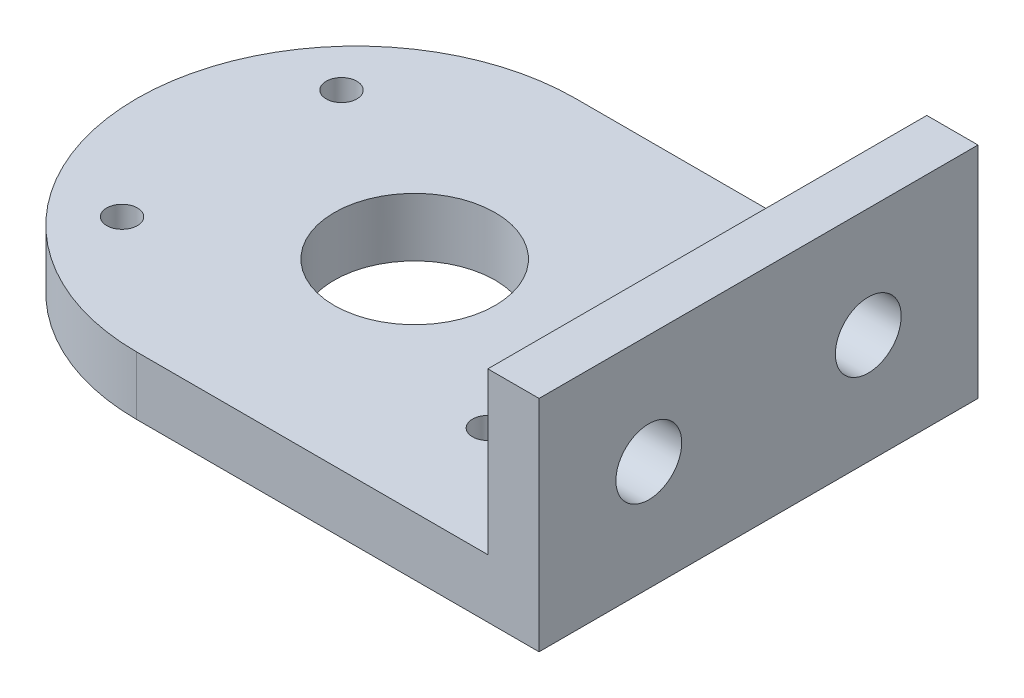
SolidWorks part; units mm, degrees
ref_plane "前视基准面" through (0, 0, 0) normal (0, 0, 1) x (1, 0, 0)
ref_plane "上视基准面" through (0, 0, 0) normal (0, 1, 0) x (1, 0, 0)
ref_plane "右视基准面" through (0, 0, 0) normal (1, 0, 0) x (0, 0, -1)
sketch "草图1" plane through (0, 0, 0) normal (0, 1, 0) x (1, 0, 0)
  line L1 (-14.75, 30) -> (40.25, 30)
  line L3 (-14.75, -30) -> (40.25, -30)
  line L4 (40.25, 30) -> (40.25, -30)
  arc A0 (-14.75, 30) -> (-14.75, -30) centre (-14.75, 0) ccw
  point P0 (0, 0)
  dimension "D4" = 55
  dimension "D1" = 60
  dimension "D2" = 40.25
  dimension "D3" = 30
extrude "凸台-拉伸1" add sketch "草图1" along normal blind 8
sketch "草图2" plane through (0, 8, 0) normal (0, 1, 0) x (1, 0, 0)
  line L0 (-14.75, -30) -> (40.25, -30) construction
  line L1 (40.25, 30) -> (33.25, 30)
  line L2 (40.25, 30) -> (40.25, -30)
  line L3 (40.25, -30) -> (33.25, -30)
  line L4 (33.25, 30) -> (33.25, -30)
  dimension "D1" = 7
extrude "凸台-拉伸2" add sketch "草图2" along normal blind 22
sketch "草图3" plane through (40.25, 0, 0) normal (1, 0, 0) x (0, 0, -1)
  line L0 (-15, 15) -> (15, 15)
  line L1 (-30, 15) -> (-27.4989, 15) construction
  line L2 (-30, 30) -> (-30, 0) construction
  point P6 (0, 15)
  dimension "D1" = 30
  dimension "D2" = 0
hole_wizard "大小mm 暗销孔1" positions "3D草图1" profile "草图4" hole size "Ø1.0" standard "GB" end condition through all
sketch3d "3D草图1"
  point P0 (40.25, 15, 15)
  point P3 (40.25, 15, -15)
sketch "草图4" plane through (40.25, 15, 15) normal (0, 1, 0) x (0, 0, -1)
  line L0 (0, 0) -> (0, 85)
  line L1 (0, 85) -> (4.5, 85)
  line L2 (4.5, 85) -> (4.5, 0)
  line L5 (4.5, 0) -> (0, 0)
  line L11 (0, -6.35) -> (0, 107.95) construction
  dimension "通孔孔直径" = 9
  dimension "通孔孔深度" = 85
sketch "草图5" plane through (0, 0, 0) normal (0, -1, 0) x (1, 0, 0)
  line L0 (40.25, 15) -> (40.25, -15) construction
  line L4 (-14.75, 30) -> (40.25, 30) construction
  circle A2 centre (-6.75, 0) radius 11
  dimension "D2" = 22
  dimension "D1" = 47
  dimension "D3" = 30
sketch "草图6" plane through (0, 0, 0) normal (0, -1, 0) x (1, 0, 0)
  line L0 (40.25, 15) -> (40.25, -15) construction
  line L1 (-31.75, 15) -> (18.25, 15)
  line L2 (-31.75, 15) -> (-31.75, -15)
  line L3 (-31.75, -15) -> (18.25, -15)
  line L4 (18.25, 15) -> (18.25, -15)
  line L5 (-31.75, 15) -> (18.25, -15) construction
  line L6 (-31.75, -15) -> (18.25, 15) construction
  point P0 (-6.75, 0)
  dimension "D1" = 30
  dimension "D2" = 50
  dimension "D3" = 22
  dimension "D4" = 15
hole_wizard "M5 螺纹孔1" positions "3D草图2" profile "草图7" tap size "M5" standard "GB" end condition through all
sketch3d "3D草图2"
  point P0 (-31.75, 0, 15)
  point P3 (18.25, 0, 15)
  point P6 (18.25, 0, -15)
  point P9 (-31.75, 0, -15)
sketch "草图7" plane through (-31.75, 0, 15) normal (1, 0, 0) x (0, 0, -1)
  line L0 (0, 0) -> (0, 30)
  line L1 (0, 30) -> (2.1, 30)
  line L2 (2.1, 30) -> (2.1, 0)
  line L5 (2.1, 0) -> (0, 0)
  line L11 (0, -6.35) -> (0, 107.95) construction
  dimension "通孔螺纹孔钻头直径" = 4.2
  dimension "通孔螺纹孔钻头深度" = 30
cosmetic thread "孔螺蚊线1" parameters "D2"=5
cosmetic thread "孔螺蚊线2" parameters "D2"=5
cosmetic thread "孔螺蚊线3" parameters "D2"=5
cosmetic thread "孔螺蚊线4" parameters "D2"=5
extrude "切除-拉伸1" cut sketch "草图5" against normal blind 10 contours A2
